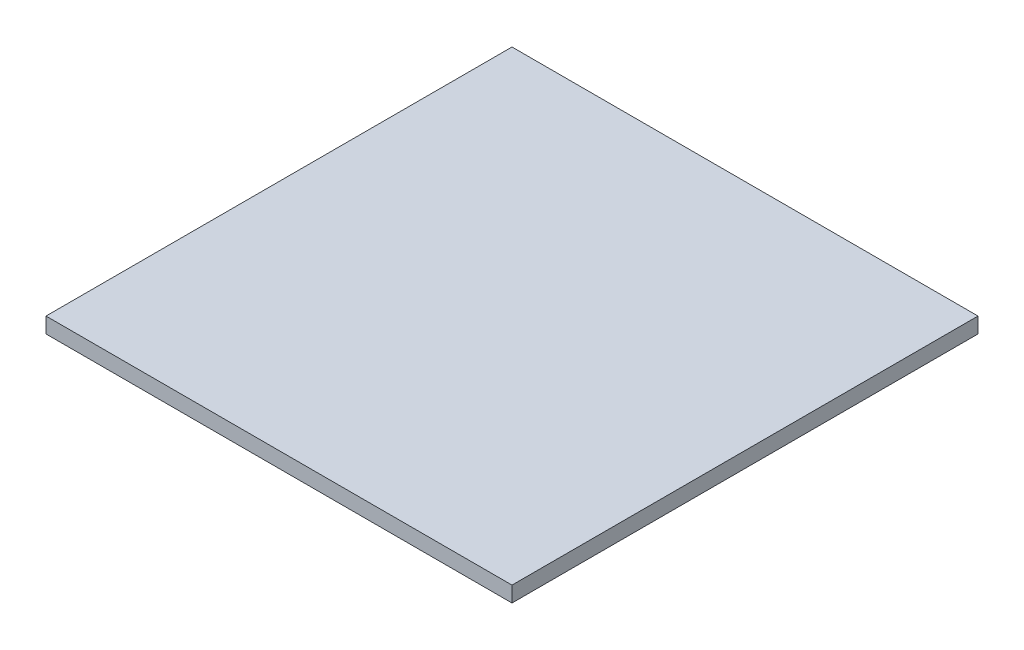
SolidWorks part; units mm, degrees
ref_plane "Front Plane" through (0, 0, 0) normal (0, 0, 1) x (1, 0, 0)
ref_plane "Top Plane" through (0, 0, 0) normal (0, 1, 0) x (1, 0, 0)
ref_plane "Right Plane" through (0, 0, 0) normal (1, 0, 0) x (0, 0, -1)
sketch "Sketch1" plane through (0, 0, 0) normal (0, 1, 0) x (1, 0, 0)
  line L1 (-46.146, 35.9083) -> (43.854, 35.9083)
  line L2 (-46.146, 35.9083) -> (-46.146, -54.0917)
  line L3 (-46.146, -54.0917) -> (43.854, -54.0917)
  line L4 (43.854, 35.9083) -> (43.854, -54.0917)
extrude "Boss-Extrude1" add sketch "Sketch1" along normal blind 3
